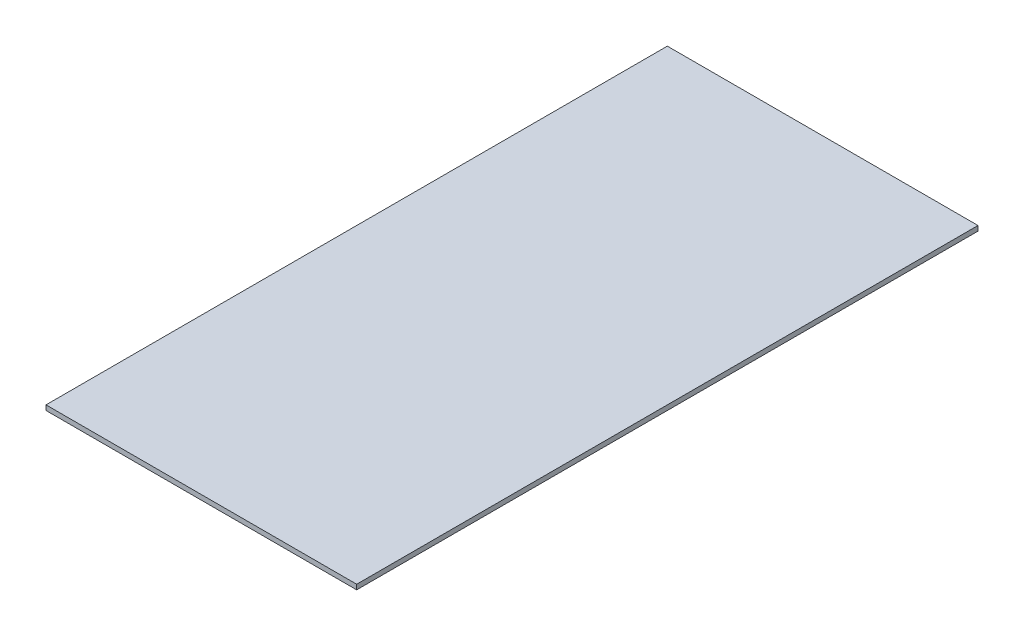
SolidWorks part; units mm, degrees
material "PW110:Mi:0:30:C1:0:1:2:Re:16:"
ref_plane "Front" through (0, 0, 0) normal (0, 0, 1) x (1, 0, 0)
ref_plane "Top" through (0, 0, 0) normal (0, 1, 0) x (1, 0, 0)
ref_plane "Right" through (0, 0, 0) normal (1, 0, 0) x (0, 0, -1)
sketch "Sketch1" plane through (0, 0, 0) normal (0, 1, 0) x (1, 0, 0)
  line L1 (-47.5, 190) -> (47.5, 190)
  line L2 (-47.5, 190) -> (-47.5, 0)
  line L3 (-47.5, 0) -> (47.5, 0)
  line L4 (47.5, 190) -> (47.5, 0)
  dimension "D1" = 190
  dimension "D2" = 95
  dimension "D3" = 47.5
  dimension "D4" = 190
extrude "Base-Extrude" add sketch "Sketch1" against normal blind 1.5
